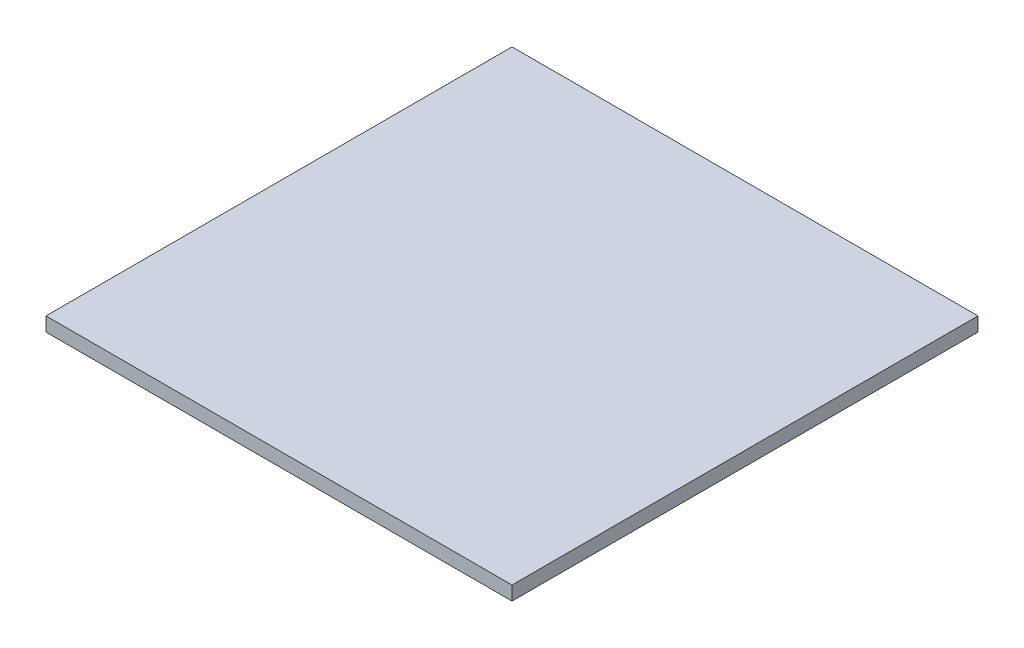
SolidWorks part; units mm, degrees
ref_plane "Front Plane" through (0, 0, 0) normal (0, 0, 1) x (1, 0, 0)
ref_plane "Top Plane" through (0, 0, 0) normal (0, 1, 0) x (1, 0, 0)
ref_plane "Right Plane" through (0, 0, 0) normal (1, 0, 0) x (0, 0, -1)
sketch "Sketch1" plane through (0, 0, 0) normal (0, 1, 0) x (1, 0, 0)
  line L1 (-50, -50) -> (50, -50)
  line L2 (-50, -50) -> (-50, 50)
  line L3 (-50, 50) -> (50, 50)
  line L4 (50, -50) -> (50, 50)
  line L5 (-50, -50) -> (50, 50) construction
  line L6 (-50, 50) -> (50, -50) construction
  point P0 (0, 0)
  dimension "D1" = 100
  dimension "D2" = 100
extrude "Boss-Extrude1" add sketch "Sketch1" along normal blind 3
sketch "Sketch2" plane through (0, 3, 0) normal (0, 1, 0) x (1, 0, 0)
  line L0 (-50, -50) -> (50, -50) construction
  line L1 (-50, 50) -> (-50, -50) construction
  line L2 (-25, -40) -> (14.646, -40)
  line L3 (-25, -40) -> (-25, 8.3) construction
  circle A0 centre (-23.4, 8.3) radius 1.6
  circle A1 centre (27.4, -7) radius 1.6
  circle A2 centre (27.4, -34.9) radius 1.6
  circle A3 centre (-25, -40) radius 1.6
  dimension "D2" = 3.2
  dimension "D5" = 50.8
  dimension "D6" = 10
  dimension "D7" = 25
  dimension "D8" = 27.9
  dimension "D9" = 5.1
  dimension "D10" = 48.3
extrude "Cut-Extrude2" [suppressed] cut sketch "Sketch2" against normal blind 3 contours A0 | A1 | A2 | A3
sketch "Sketch3" [suppressed] plane through (0, 0, 0) normal (0, -1, 0) x (1, 0, 0)
  line L0 (32.7, 6.7) -> (32.7, -4.3) construction
  line L1 (32.2, -4.8) -> (22.7, -4.8) construction
  line L2 (22.7, 7.2) -> (32.2, 7.2) construction
  line L3 (22.2, -4.3) -> (22.2, 6.7) construction
  line L4 (32.7, 6.7) -> (32.7, -4.3) construction
  line L5 (32.2, -4.8) -> (22.7, -4.8) construction
  line L6 (22.7, 7.2) -> (32.2, 7.2) construction
  line L7 (22.2, -4.3) -> (22.2, 6.7) construction
  line L8 (21.2, -4.3) -> (21.2, 6.7)
  line L9 (22.7, 8.2) -> (32.2, 8.2)
  line L10 (33.7, 6.7) -> (33.7, -4.3)
  line L11 (32.2, -5.8) -> (22.7, -5.8)
  arc A0 (32.7, 6.7) -> (32.2, 7.2) centre (32.2, 6.7) ccw construction
  arc A1 (32.2, -4.8) -> (32.7, -4.3) centre (32.2, -4.3) ccw construction
  arc A2 (22.7, 7.2) -> (22.2, 6.7) centre (22.7, 6.7) ccw construction
  arc A3 (22.2, -4.3) -> (22.7, -4.8) centre (22.7, -4.3) ccw construction
  arc A4 (32.7, 6.7) -> (32.2, 7.2) centre (32.2, 6.7) ccw construction
  arc A5 (32.2, -4.8) -> (32.7, -4.3) centre (32.2, -4.3) ccw construction
  arc A6 (22.7, 7.2) -> (22.2, 6.7) centre (22.7, 6.7) ccw construction
  arc A7 (22.2, -4.3) -> (22.7, -4.8) centre (22.7, -4.3) ccw construction
  arc A8 (22.7, 8.2) -> (21.2, 6.7) centre (22.7, 6.7) ccw
  arc A9 (33.7, 6.7) -> (32.2, 8.2) centre (32.2, 6.7) ccw
  arc A10 (32.2, -5.8) -> (33.7, -4.3) centre (32.2, -4.3) ccw
  arc A11 (21.2, -4.3) -> (22.7, -5.8) centre (22.7, -4.3) ccw
  dimension "D1" = 1
extrude "Cut-Extrude3" [suppressed] cut sketch "Sketch3" against normal through all
